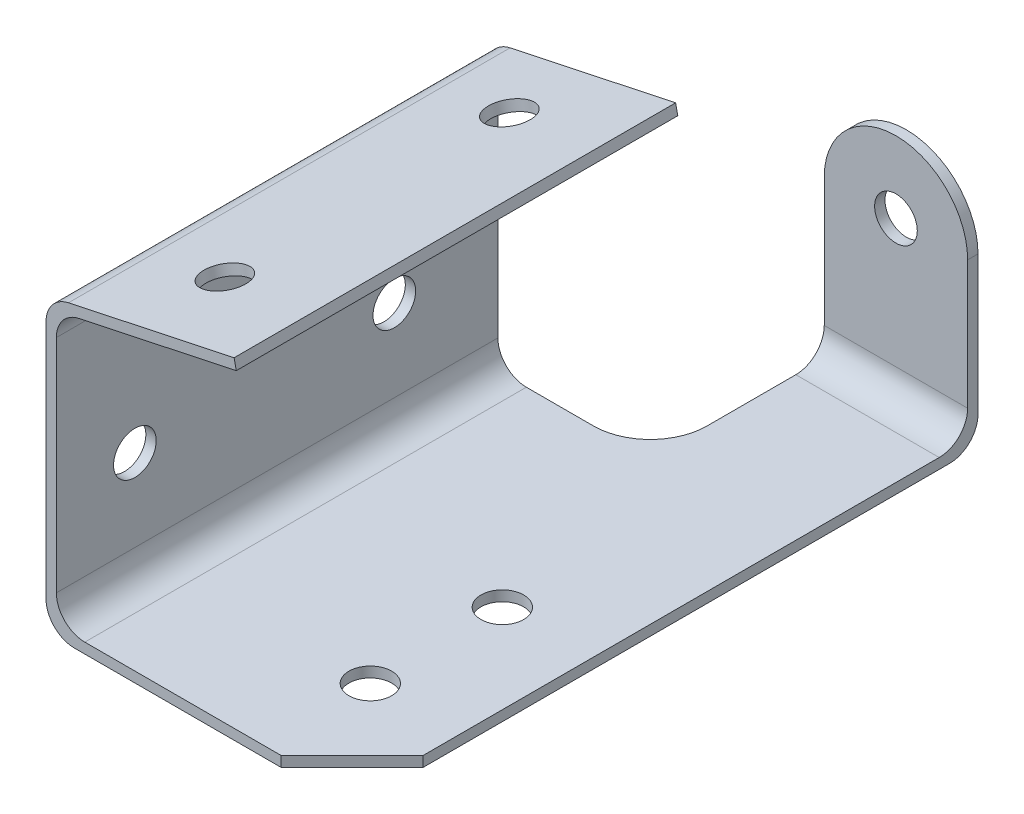
SolidWorks part; units mm, degrees
ref_plane "Front Plane" through (0, 0, 0) normal (0, 0, 1) x (1, 0, 0)
ref_plane "Top Plane" through (0, 0, 0) normal (0, 1, 0) x (1, 0, 0)
ref_plane "Right Plane" through (0, 0, 0) normal (1, 0, 0) x (0, 0, -1)
sketch "Sketch1" plane through (0, 0, 0) normal (0, 0, 1) x (1, 0, 0)
  line L0 (6.35, 0) -> (68.326, 0)
  line L1 (0, 6.35) -> (0, 59.8819)
  line L2 (5.0298, 66.0931) -> (41.988, 73.9488)
  line L3 (0, 65.024) -> (0, 73.9488) construction
  line L4 (41.988, 73.9488) -> (42.4685, 71.6879)
  line L5 (42.4685, 71.6879) -> (7.3412, 64.2214)
  line L6 (2.3114, 58.0101) -> (2.3114, 8.6614)
  line L7 (8.6614, 2.3114) -> (68.326, 2.3114)
  line L8 (68.326, 2.3114) -> (68.326, 0)
  arc A0 (6.35, 0) -> (0, 6.35) centre (6.35, 6.35) cw
  arc A1 (2.3114, 8.6614) -> (8.6614, 2.3114) centre (8.6614, 8.6614) ccw
  arc A2 (2.3114, 58.0101) -> (7.3412, 64.2214) centre (8.6614, 58.0101) cw
  arc A3 (0, 59.8819) -> (5.0298, 66.0931) centre (6.35, 59.8819) cw
  point P12 (0, 0)
  dimension "D8" = 6.35
  dimension "D1" = 68.326
  dimension "D2" = 65.024
  dimension "D3" = 78
  dimension "D4" = 42.926
  dimension "D5" = 2.3114
  dimension "D6" = 2.3114
  dimension "D7" = 2.3114
extrude "Boss-Extrude1" add sketch "Sketch1" against normal blind 98.552
sketch "Sketch2" plane through (68.326, 0, 0) normal (1, 0, 0) x (0, 0, -1)
  line L0 (98.552, 0) -> (133.35, 0)
  line L1 (139.7, 6.35) -> (139.7, 53.34)
  line L2 (139.7, 53.34) -> (137.3886, 53.34)
  line L3 (137.3886, 53.34) -> (137.3886, 8.6614)
  line L4 (131.0386, 2.3114) -> (98.552, 2.3114)
  line L9 (0, 2.3114) -> (0, 0)
  line L10 (0, 0) -> (98.552, 0)
  line L11 (98.552, 0) -> (98.552, 2.3114)
  line L12 (98.552, 2.3114) -> (0, 2.3114)
  line L15 (98.552, 0) -> (98.552, 2.3114)
  arc A0 (133.35, 0) -> (139.7, 6.35) centre (133.35, 6.35) ccw
  arc A1 (137.3886, 8.6614) -> (131.0386, 2.3114) centre (131.0386, 8.6614) cw
  point P12 (139.7, 0)
  dimension "D3" = 6.35
  dimension "D1" = 2.3114
  dimension "D2" = 139.7
  dimension "D4" = 53.34
  dimension "D5" = 0
extrude "Boss-Extrude2" add sketch "Sketch2" against normal blind 32.004 contours L3 A1 L4 L15 L0 A0 L1 L2
sketch "Sketch3" plane through (0, 0, -137.3886) normal (0, 0, 1) x (1, 0, 0)
  line L0 (36.322, 53.34) -> (68.326, 53.34) construction
  line L1 (6.35, 0) -> (68.326, 0) construction
  line L2 (52.324, 8.6614) -> (52.324, 37.338) construction
  line L3 (36.322, 8.6614) -> (68.326, 8.6614) construction
  line L4 (36.322, 37.338) -> (68.326, 37.338) construction
  line L5 (36.322, 37.338) -> (36.322, 53.34)
  line L6 (36.322, 53.34) -> (68.326, 53.34)
  line L7 (68.326, 53.34) -> (68.326, 37.338)
  line L9 (36.322, 53.34) -> (36.322, 8.6614) construction
  circle A0 centre (52.324, 37.338) radius 16.002
  circle A1 centre (52.324, 37.338) radius 4.7625
  line M2 (68.326, 8.6614) -> (68.326, 53.34)
  line M3 (68.326, 53.34) -> (36.322, 53.34)
  line M4 (36.322, 53.34) -> (36.322, 8.6614)
  dimension "D1" = 32.004
  dimension "D3" = 9.525
  dimension "D2" = 37.338
extrude "Cut-Extrude1" cut sketch "Sketch3" against normal through all contours A0 L6 M4 | A0 M2 M3 | A1
fillet "Fillet1" radius 12.7 1 edges
sketch "Sketch4" plane through (0, 2.3114, 0) normal (0, 1, 0) x (1, 0, 0)
  line L0 (68.326, 131.0386) -> (68.326, 0) construction
  line L1 (68.326, 0) -> (8.6614, 0) construction
  line L2 (52.451, 0) -> (68.326, 15.875)
  line L3 (68.326, 15.875) -> (68.326, 0)
  line L4 (68.326, 0) -> (52.451, 0)
  circle A0 centre (48.514, 23.876) radius 4.7625
  circle A1 centre (48.514, 53.34) radius 4.7625
  dimension "D2" = 9.525
  dimension "D1" = 19.812
  dimension "D3" = 29.464
  dimension "D4" = 23.876
  dimension "D5" = 45
  dimension "D6" = 15.875
extrude "Cut-Extrude2" cut sketch "Sketch4" against normal through all
sketch "Sketch5" plane through (2.3114, 0, 0) normal (1, 0, 0) x (0, 0, -1)
  line L0 (0, 8.6614) -> (0, 58.0101) construction
  line L1 (98.552, 8.6614) -> (98.552, 58.0101) construction
  line L2 (98.552, 8.6614) -> (0, 8.6614) construction
  circle A0 centre (17.526, 26.9494) radius 4.7625
  circle A1 centre (75.438, 26.9494) radius 4.7625
  circle A2 centre (17.526, 56.4134) radius 4.7625
  circle A3 centre (75.438, 56.4134) radius 4.7625
  dimension "D4" = 9.525
  dimension "D1" = 17.526
  dimension "D2" = 23.114
  dimension "D3" = 18.288
  dimension "D5" = 29.464
extrude "Cut-Extrude3" cut sketch "Sketch5" against normal through all and the other way through all
sketch "Sketch6" plane through (-13.2238, 62.2132, 0) normal (-0.2079, 0.9781, 0) x (0.9781, 0.2079, 0)
  line L0 (56.4452, 98.552) -> (18.6614, 98.552) construction
  line L1 (56.4452, 98.552) -> (56.4452, 0) construction
  circle A0 centre (34.8552, 82.55) radius 4.7625
  circle A1 centre (34.8552, 19.05) radius 4.7625
  dimension "D1" = 9.525
  dimension "D2" = 16.002
  dimension "D3" = 63.5
  dimension "D4" = 21.59
extrude "Cut-Extrude4" cut sketch "Sketch6" against normal up to next
